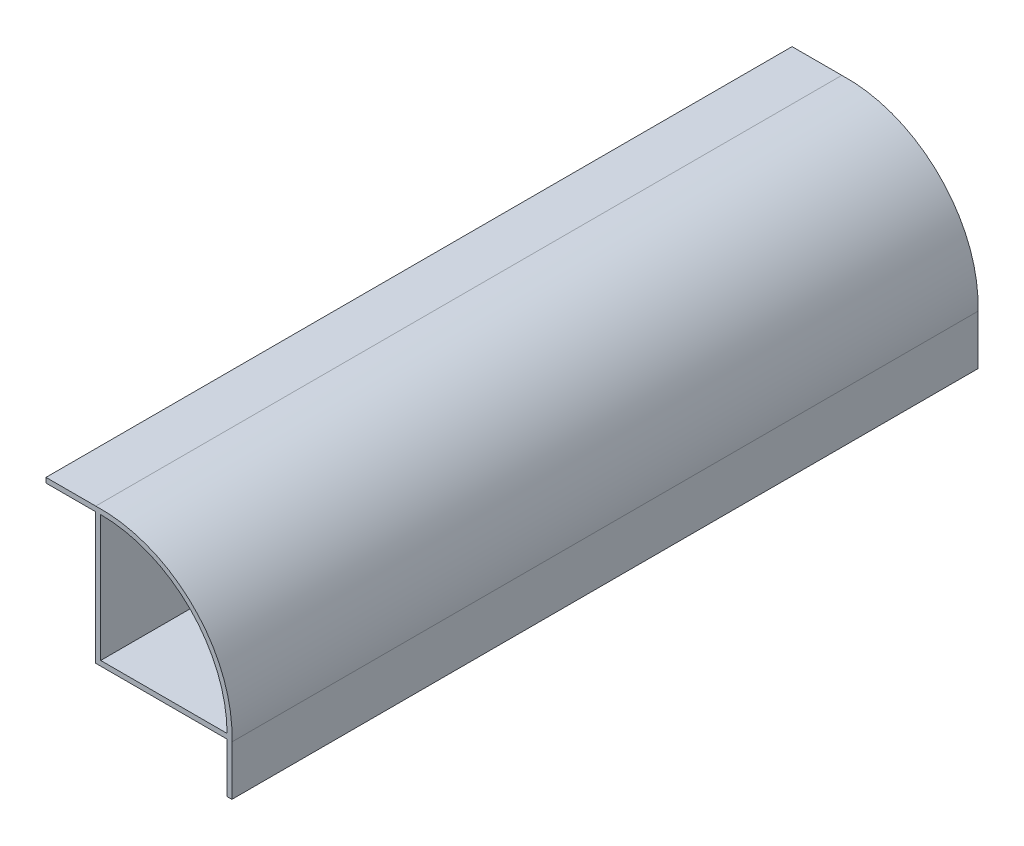
SolidWorks part; units mm, degrees
ref_plane "Alzado" through (0, 0, 0) normal (0, 0, 1) x (1, 0, 0)
ref_plane "Planta" through (0, 0, 0) normal (0, 1, 0) x (1, 0, 0)
ref_plane "Vista lateral" through (0, 0, 0) normal (1, 0, 0) x (0, 0, -1)
sketch "Croquis1" plane through (0, 0, 0) normal (0, 0, 1) x (1, 0, 0)
  line L0 (-13.7, -13.7) -> (13.6811, -13.7)
  line L1 (-12.7, -12.7) -> (12.7, -12.7)
  line L2 (-12.7, -12.7) -> (-12.7, 12.7)
  line L5 (0, 16.5842) -> (0, -23.118) construction
  line L6 (-13.7, -13.7) -> (-13.7, 13.6811)
  line L8 (-18.0998, 0) -> (17.5647, 0) construction
  line L9 (13.6811, -13.7) -> (12.6811, -13.7)
  line L10 (13.6811, -13.7) -> (13.6811, -23.7)
  line L11 (13.6811, -23.7) -> (12.6811, -23.7)
  line L12 (12.6811, -13.7) -> (12.6811, -23.7)
  line L13 (-13.7, 13.6811) -> (-23.7, 13.6811)
  line L14 (-13.7, 13.6811) -> (-13.7, 12.6811)
  line L15 (-13.7, 12.6811) -> (-23.7, 12.6811)
  line L16 (-23.7, 13.6811) -> (-23.7, 12.6811)
  arc A0 (-12.7, 12.7) -> (12.7, -12.7) centre (-12.7, -12.7) cw
  arc A1 (-13.7, 13.6811) -> (13.6811, -13.7) centre (-12.7, -12.7) cw
  point P0 (0, 0)
  point P12 (-12.7, 0)
  point P13 (0, -12.7)
  dimension "D3" = 25.4
  dimension "D1" = 25.4
  dimension "D2" = 25.4
  dimension "D5" = 1
  dimension "D6" = 10
  dimension "D7" = 1
  dimension "D8" = 10
  dimension "D4" = 1
extrude "Saliente-Extruir1" add sketch "Croquis1" along normal mid plane 150 contours A1 L6 L0 L2 A0 L1 | L13 L16 L15 L6 | L0 L12 L11 L10
ref_plane "Plano1" through (-12.7, -12.7, 75) normal (0, 1, 0) x (1, 0, 0)
